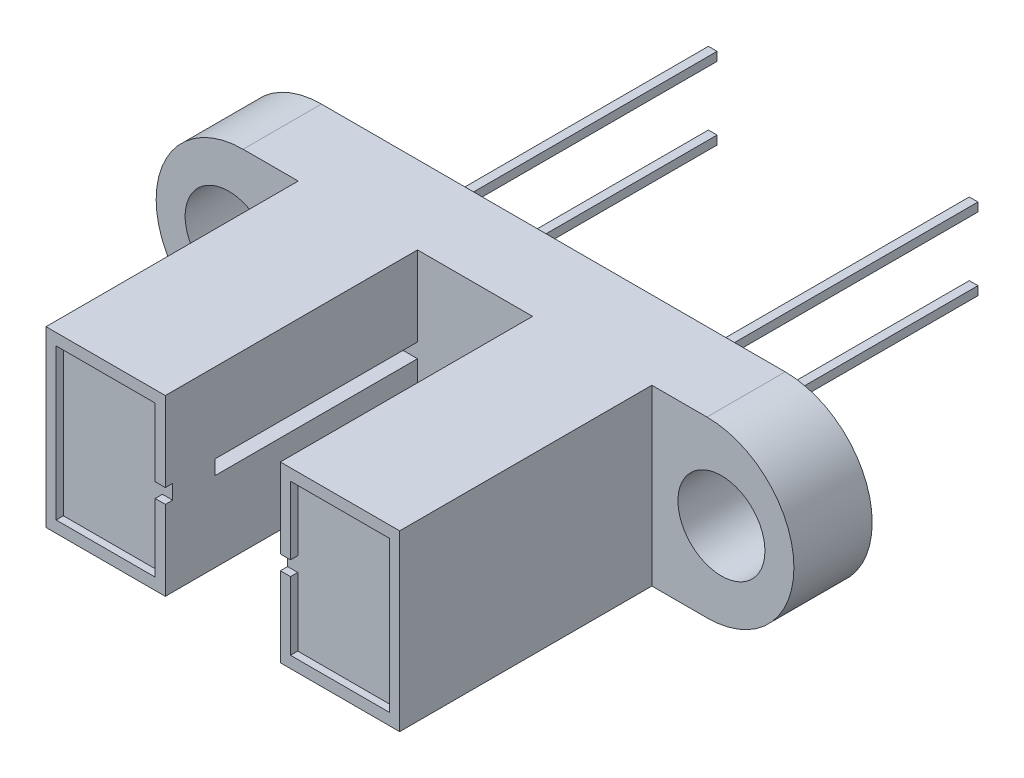
SolidWorks part; units mm, degrees
ref_plane "Front Plane" through (0, 0, 0) normal (0, 0, 1) x (1, 0, 0)
ref_plane "Top Plane" through (0, 0, 0) normal (0, 1, 0) x (1, 0, 0)
ref_plane "Right Plane" through (0, 0, 0) normal (1, 0, 0) x (0, 0, -1)
sketch "Sketch1" plane through (0, 0, 0) normal (0, 0, 1) x (1, 0, 0)
  line L0 (-8, 0) -> (8, 0) construction
  line L1 (-8, 3) -> (8, 3)
  line L2 (-8, -3) -> (8, -3)
  line L3 (-11, 11.7692) -> (-11, -12.4154) construction
  line L4 (11, 12.4154) -> (11, -13.6154) construction
  arc A0 (-8, 3) -> (-8, -3) centre (-8, 0) ccw
  arc A1 (8, -3) -> (8, 3) centre (8, 0) ccw
  point P3 (0, 0)
  dimension "D2" = 22
  dimension "D1" = 6
extrude "Boss-Extrude1" add sketch "Sketch1" along normal blind 2.7
sketch "Sketch2" plane through (0, 0, 2.7) normal (0, 0, 1) x (1, 0, 0)
  line L0 (0, 0) -> (0, 7.0288) construction
  circle A0 centre (-8.5, 0) radius 1.5
  circle A1 centre (8.5, 0) radius 1.5
  dimension "D1" = 3
  dimension "D2" = 17
extrude "Cut-Extrude1" cut sketch "Sketch2" against normal through all
sketch "Sketch3" plane through (0, 0, 2.7) normal (0, 0, 1) x (1, 0, 0)
  line L0 (8, 3) -> (-8, 3) construction
  line L1 (-6.1, 3) -> (-1.9844, 3)
  line L2 (-6.1, 3) -> (-6.1, -3)
  line L3 (-6.1, -3) -> (-1.9844, -3)
  line L4 (-1.9844, 3) -> (-1.9844, -3)
  line L5 (-8, -3) -> (8, -3) construction
  line L6 (0, 0) -> (0, 4.7115) construction
  line L7 (6.1, 3) -> (1.9844, 3)
  line L8 (6.1, 3) -> (6.1, -3)
  line L9 (6.1, -3) -> (1.9844, -3)
  line L10 (1.9844, 3) -> (1.9844, -3)
  dimension "D1" = 3.9688
  dimension "D2" = 12.2
extrude "Boss-Extrude2" add sketch "Sketch3" along normal blind 8.7
sketch "Sketch4" plane through (0, 0, 0) normal (0, 0, -1) x (-1, 0, 0)
  line L1 (6, 1.5) -> (-6, 1.5)
  line L2 (6, 1.5) -> (6, -1.5)
  line L3 (6, -1.5) -> (-6, -1.5)
  line L4 (-6, 1.5) -> (-6, -1.5)
  line L5 (6, 1.5) -> (-6, -1.5) construction
  line L6 (6, -1.5) -> (-6, 1.5) construction
  point P0 (0, 0)
  dimension "D1" = 3
  dimension "D2" = 12
extrude "Cut-Extrude2" cut sketch "Sketch4" against normal blind 2
sketch "Sketch5" plane through (0, 0, 11.4) normal (0, 0, 1) x (1, 0, 0)
  line L10 (-1.9844, 3) -> (-6.1, 3) construction
  line L11 (-1.9844, -3) -> (-1.9844, 3) construction
  line L12 (-6.1, 3) -> (-6.1, -3) construction
  line L13 (-6.1, -3) -> (-1.9844, -3) construction
  line L14 (-1.9844, -3) -> (-1.9844, 3) construction
  line L15 (-2.3344, 0.25) -> (-1.9844, 0.25)
  line L17 (-2.3344, -0.25) -> (-1.9844, -0.25)
  line L18 (-2.3344, -2.6) -> (-2.3344, -0.25)
  line L19 (-5.75, -2.6) -> (-2.3344, -2.6)
  line L20 (-2.3344, 2.6) -> (-5.75, 2.6)
  line L21 (-5.75, 2.6) -> (-5.75, -2.6)
  line L22 (-1.9844, 0.25) -> (-1.9844, -0.25)
  line L23 (-2.3344, 0.25) -> (-2.3344, 2.6)
  line L24 (0, 0) -> (-1.036, 0) construction
  dimension "D1" = 0.4
  dimension "D2" = 0.35
  dimension "D3" = 0.35
  dimension "D4" = 0.4
  dimension "D5" = 0.5
extrude "Cut-Extrude3" cut sketch "Sketch5" against normal blind 0.25
mirror "Mirror1" about plane through (0, 0, 0) normal (1, 0, 0) of "Cut-Extrude3"
sketch "Sketch6" plane through (0, 0, 2) normal (0, 0, -1) x (-1, 0, 0)
  line L0 (0, 0) -> (0, 1.9023) construction
  line L1 (0, 0) -> (-0.931, 0) construction
  line L6 (-4.65, 1.4) -> (-4.35, 1.4)
  line L7 (-4.65, 1.4) -> (-4.65, 1.1)
  line L8 (-4.65, 1.1) -> (-4.35, 1.1)
  line L9 (-4.35, 1.4) -> (-4.35, 1.1)
  line L10 (-4.65, 1.4) -> (-4.35, 1.1) construction
  line L11 (-4.65, 1.1) -> (-4.35, 1.4) construction
  point P7 (-4.5, 1.25)
  dimension "D1" = 0.3
  dimension "D2" = 4.5
  dimension "D3" = 1.25
extrude "Boss-Extrude3" add sketch "Sketch6" along normal blind 12
pattern_linear "LPattern1" count 2 spacing 2.5 along (0, -1, 0) count 2 spacing 9 along (-1, 0, 0) of "Boss-Extrude3"
sketch "Sketch7" plane through (1.9844, 0, 0) normal (-1, 0, 0) x (0, 0, 1)
  line L0 (2.7, 3) -> (2.7, -3) construction
  line L1 (2.7, 0.25) -> (9.68, 0.25)
  line L2 (2.7, 0.25) -> (2.7, -0.25)
  line L3 (2.7, -0.25) -> (9.68, -0.25)
  line L4 (9.68, 0.25) -> (9.68, -0.25)
  line L5 (2.7, 0.25) -> (9.68, -0.25) construction
  line L6 (2.7, -0.25) -> (9.68, 0.25) construction
  line L7 (11.4, 3) -> (11.4, -3) construction
  point P0 (6.19, 0)
  dimension "D1" = 1.72
  dimension "D2" = 0.5
extrude "Cut-Extrude4" cut sketch "Sketch7" against normal blind 1
mirror "Mirror2" about plane through (0, 0, 0) normal (1, 0, 0) of "Cut-Extrude4"
